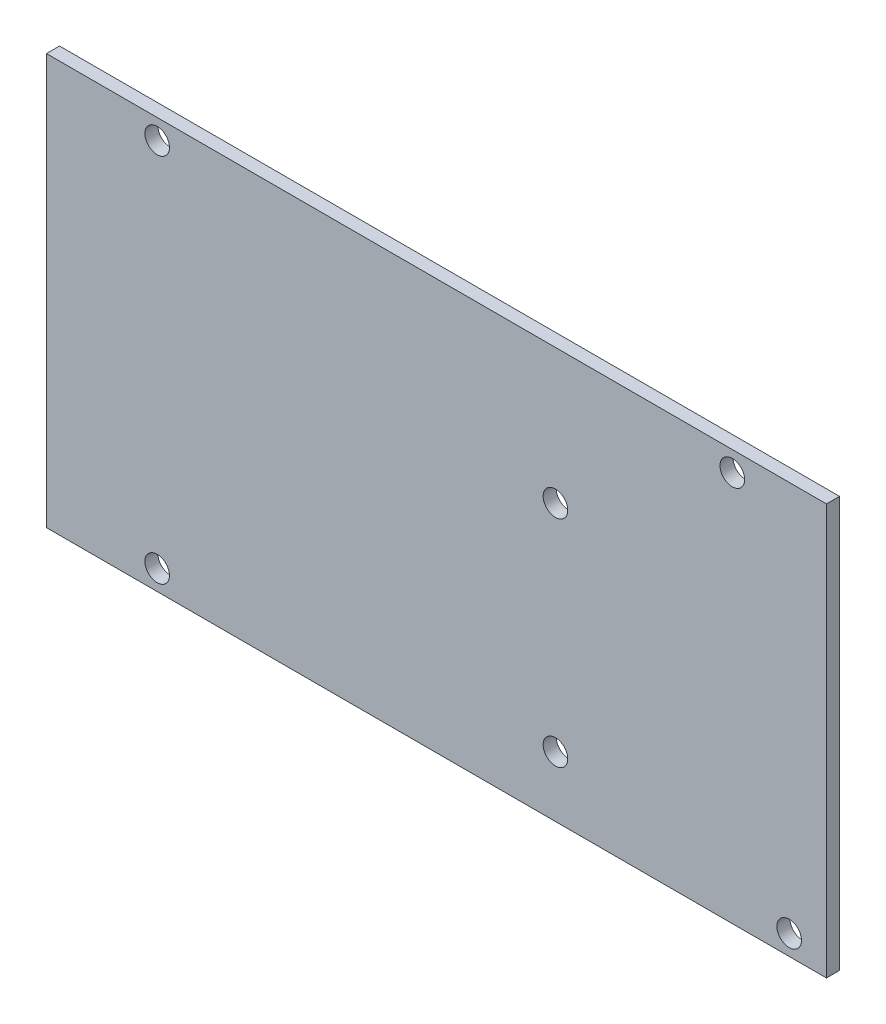
SolidWorks part; units mm, degrees
ref_plane "Front Plane" through (0, 0, 0) normal (0, 0, 1) x (1, 0, 0)
ref_plane "Top Plane" through (0, 0, 0) normal (0, 1, 0) x (1, 0, 0)
ref_plane "Right Plane" through (0, 0, 0) normal (1, 0, 0) x (0, 0, -1)
sketch "Sketch1" plane through (0, 0, 0) normal (0, 0, 1) x (1, 0, 0)
  line L1 (-50.725, -26.7) -> (50.725, -26.7)
  line L2 (-50.725, -26.7) -> (-50.725, 26.7)
  line L3 (-50.725, 26.7) -> (50.725, 26.7)
  line L4 (50.725, -26.7) -> (50.725, 26.7)
  line L5 (-50.725, -26.7) -> (50.725, 26.7) construction
  line L6 (-50.725, 26.7) -> (50.725, -26.7) construction
  circle A0 centre (-36.325, 24.1) radius 1.6
  circle A1 centre (-36.325, -24.1) radius 1.6
  circle A2 centre (15.475, -18.85) radius 1.6
  circle A3 centre (15.475, 9.15) radius 1.6
  circle A4 centre (38.475, 24.1) radius 1.6
  circle A5 centre (45.875, -24.1) radius 1.6
  point P0 (0, 0)
  dimension "D3" = 3.2
  dimension "D1" = 53.4
  dimension "D2" = 101.45
  dimension "D4" = 2.6
  dimension "D5" = 14.4
  dimension "D6" = 2.6
  dimension "D7" = 74.8
  dimension "D8" = 82.2
  dimension "D9" = 28
  dimension "D10" = 7.85
  dimension "D11" = 35.25
extrude "Boss-Extrude1" add sketch "Sketch1" along normal blind 1.7
